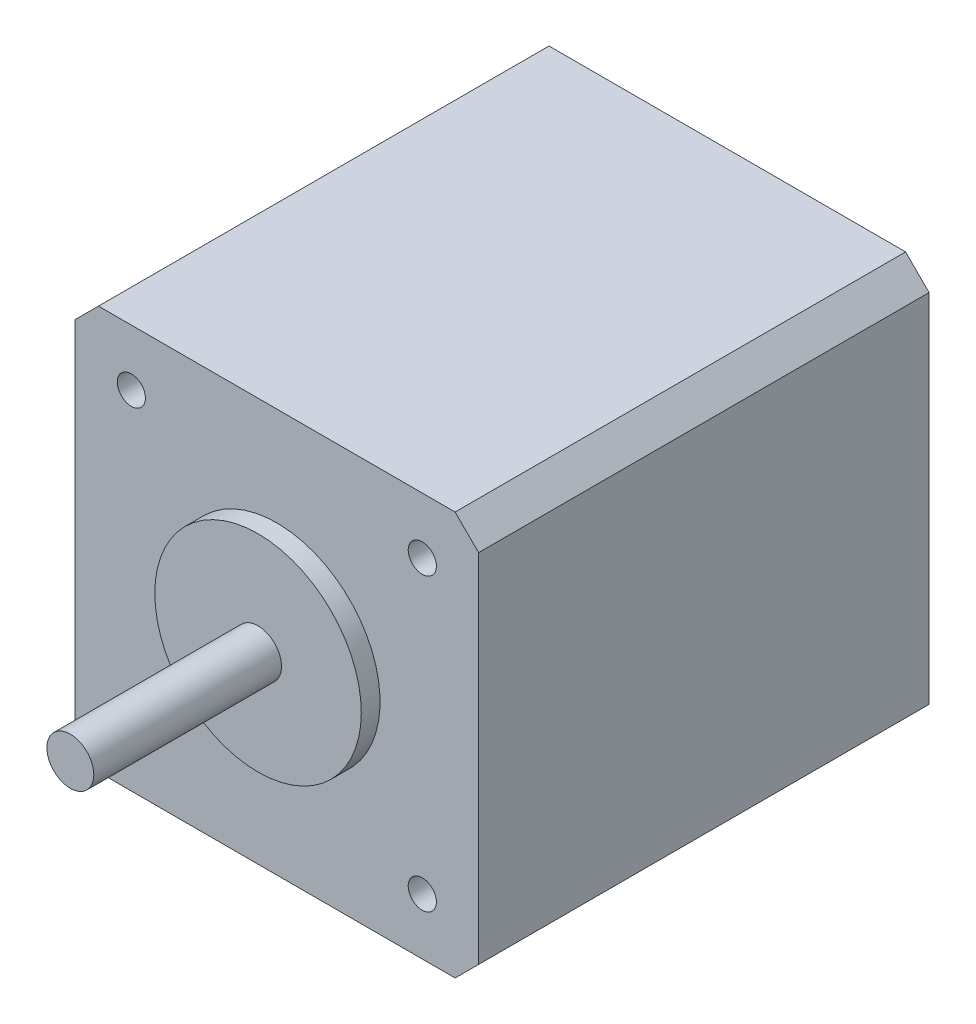
SolidWorks part; units mm, degrees
ref_plane "Front Plane" through (0, 0, 0) normal (0, 0, 1) x (1, 0, 0)
ref_plane "Top Plane" through (0, 0, 0) normal (0, 1, 0) x (1, 0, 0)
ref_plane "Right Plane" through (0, 0, 0) normal (1, 0, 0) x (0, 0, -1)
sketch "Sketch1" plane through (0, 0, 0) normal (0, 0, 1) x (1, 0, 0)
  line L1 (-21.5, -21.5) -> (21.5, -21.5)
  line L2 (-21.5, -21.5) -> (-21.5, 21.5)
  line L3 (-21.5, 21.5) -> (21.5, 21.5)
  line L4 (21.5, -21.5) -> (21.5, 21.5)
  line L5 (-21.5, -21.5) -> (21.5, 21.5) construction
  line L6 (-21.5, 21.5) -> (21.5, -21.5) construction
  point P0 (0, 0)
extrude "Boss-Extrude1" add sketch "Sketch1" along normal blind 48
chamfer "Chamfer1" distance 2.5 angle 45 4 edges at (-21.5, -21.5, 24) (21.5, -21.5, 24) (-21.5, 21.5, 24) (21.5, 21.5, 24)
sketch "Sketch2" plane through (0, 0, 48) normal (0, 0, 1) x (1, 0, 0)
  circle A0 centre (0, 0) radius 11
extrude "Boss-Extrude2" add sketch "Sketch2" along normal blind 2
sketch "Sketch3" plane through (0, 0, 50) normal (0, 0, 1) x (1, 0, 0)
  circle A0 centre (0, 0) radius 2.5
extrude "Boss-Extrude3" add sketch "Sketch3" along normal blind 20
sketch "Sketch4" plane through (0, 0, 48) normal (0, 0, 1) x (1, 0, 0)
  line L2 (19, 21.5) -> (-19, 21.5) construction
  line L3 (-21.5, 19) -> (-21.5, -19) construction
  circle A0 centre (-15.5, 15.5) radius 1.5
  circle A1 centre (15.5, 15.5) radius 1.5
  circle A2 centre (15.5, -15.5) radius 1.5
  circle A3 centre (-15.5, -15.5) radius 1.5
  dimension "D3" = 4
  dimension "D1" = 6
  dimension "D2" = 6
extrude "Cut-Extrude1" cut sketch "Sketch4" against normal blind 10
